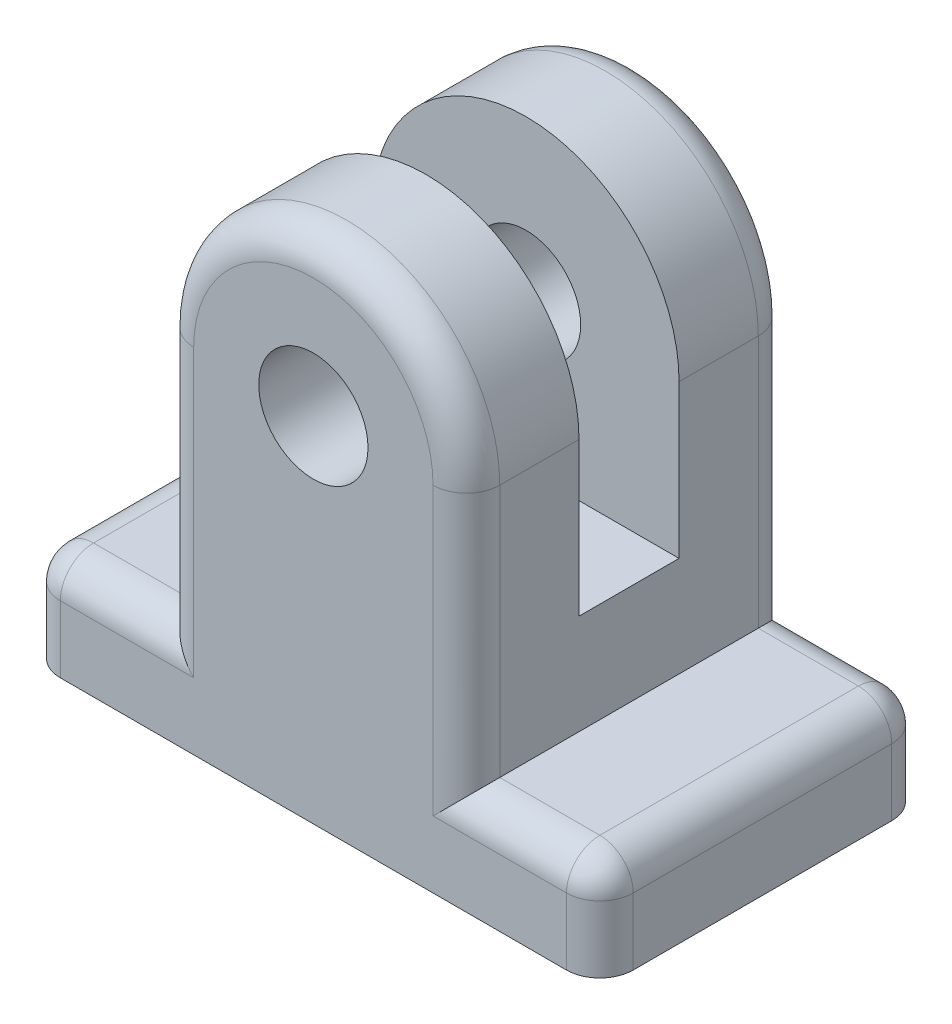
SolidWorks part; units mm, degrees
material "ABS"
ref_plane "Front Plane" through (0, 0, 0) normal (0, 0, 1) x (1, 0, 0)
ref_plane "Top Plane" through (0, 0, 0) normal (0, 1, 0) x (1, 0, 0)
ref_plane "Right Plane" through (0, 0, 0) normal (1, 0, 0) x (0, 0, -1)
sketch "Sketch1" plane through (0, 0, 0) normal (0, 0, 1) x (1, 0, 0)
  line L0 (-4.5875, 0) -> (-4.5875, -7.5875)
  line L1 (0, 0) -> (0, 4.5875) construction
  line L2 (-4.5875, -7.5875) -> (-8.5875, -7.5875)
  line L3 (-8.5875, -7.5875) -> (-8.5875, -10.5875)
  line L4 (-8.5875, -10.5875) -> (8.5875, -10.5875)
  line L5 (8.5875, -7.5875) -> (8.5875, -10.5875)
  line L6 (4.5875, -7.5875) -> (8.5875, -7.5875)
  line L7 (4.5875, 0) -> (4.5875, -7.5875)
  circle A0 centre (0, 0) radius 1.6375
  arc A1 (4.5875, 0) -> (-4.5875, 0) centre (0, 0) ccw
  point P11 (0, -10.5875)
  dimension "D1" = 3.275
  dimension "D2" = 4.5875
  dimension "D3" = 3
  dimension "D4" = 4
  dimension "D5" = 7.5875
extrude "Boss-Extrude1" add sketch "Sketch1" along normal mid plane 9.75
sketch "Sketch3" plane through (0, 0, 0) normal (0, 0, 1) x (1, 0, 0)
  line L0 (-4.5875, 0) -> (-4.5875, -4.5875)
  line L1 (-4.5875, -4.5875) -> (4.5875, -4.5875)
  line L2 (4.5875, -4.5875) -> (4.5875, 0)
  arc A0 (4.5875, 0) -> (-4.5875, 0) centre (0, 0) ccw construction
  circle A1 centre (0, 0) radius 1.6375 construction
  arc A2 (4.5875, 0) -> (-4.5875, 0) centre (0, 0) ccw
  circle A3 centre (0, 0) radius 1.6375
  dimension "D1" = 4.5875
extrude "Cut-Extrude1" cut sketch "Sketch3" against normal mid plane 3
fillet "Fillet1" radius 1 16 edges at (-8.5875, -9.0875, -4.875) (-6.5875, -7.5875, -4.875) (-8.5875, -7.5875, 0) (-8.5875, -9.0875, 4.875) (-6.5875, -7.5875, 4.875) (6.5875, -7.5875, -4.875) (8.5875, -9.0875, -4.875) (8.5875, -9.0875, 4.875) (8.5875, -7.5875, 0) (6.5875, -7.5875, 4.875) (-4.5875, -3.7938, -4.875) (0, 4.5875, -4.875) (4.5875, -3.7938, -4.875) (4.5875, -3.7938, 4.875) (0, 4.5875, 4.875) (-4.5875, -3.7938, 4.875)
equation "\"D1@Sketch1\"=\"pin diameter@values@params_print.sldprt\"+\"print fit@values@params_print.sldprt\""
equation "\"D2@Sketch1\"=\"width keep@values@params_print.sldprt\"+\"pin diameter@values@params_print.sldprt\"/2"
equation "\"D3@Sketch1\"=\"width keep@values@params_print.sldprt\""
equation "\"D4@Sketch1\"=\"width tab@values@params_print.sldprt\""
equation "\"D5@Sketch1\"=\"pin diameter@values@params_print.sldprt\"/2+2*\"width keep@values@params_print.sldprt\""
equation "\"D1@Sketch3\"=\"width keep@values@params_print.sldprt\"+\"pin diameter@values@params_print.sldprt\"/2"
